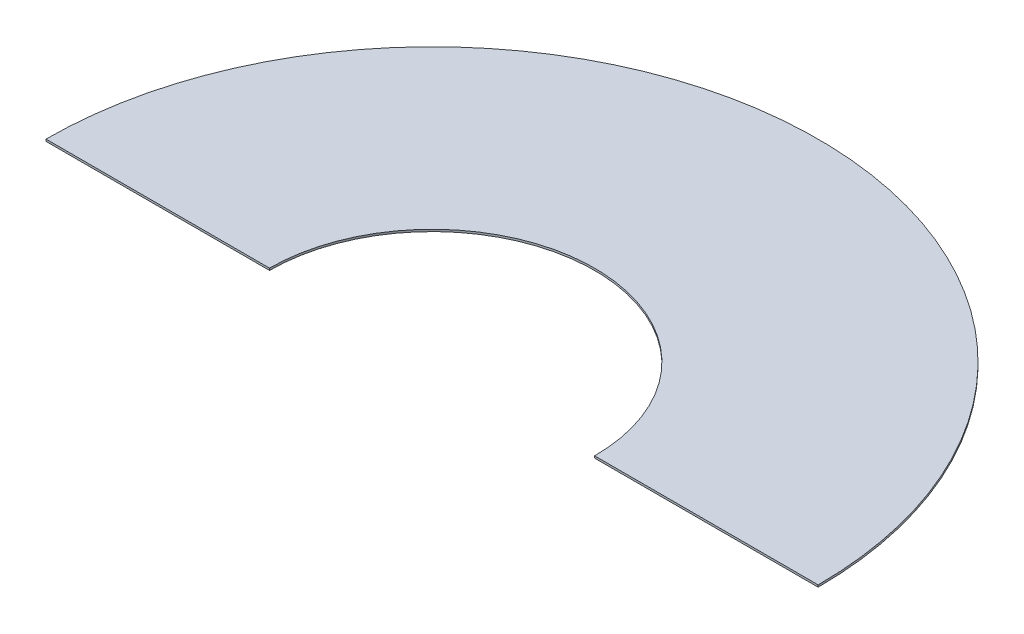
SolidWorks part; units mm, degrees
ref_plane "Front Plane" through (0, 0, 0) normal (0, 0, 1) x (1, 0, 0)
ref_plane "Top Plane" through (0, 0, 0) normal (0, 1, 0) x (1, 0, 0)
ref_plane "Right Plane" through (0, 0, 0) normal (1, 0, 0) x (0, 0, -1)
sketch "Sketch1" plane through (0, 0, 0) normal (0, 1, 0) x (1, 0, 0)
  line L0 (-380, 0) -> (-160, 0)
  line L1 (160, 0) -> (380, 0)
  arc A0 (380, 0) -> (-380, 0) centre (0, 0) ccw
  arc A1 (160, 0) -> (-160, 0) centre (0, 0) ccw
  dimension "D1" = 380
  dimension "D2" = 160
  dimension "D3" = 220
extrude "Boss-Extrude1" add sketch "Sketch1" along normal blind 2
